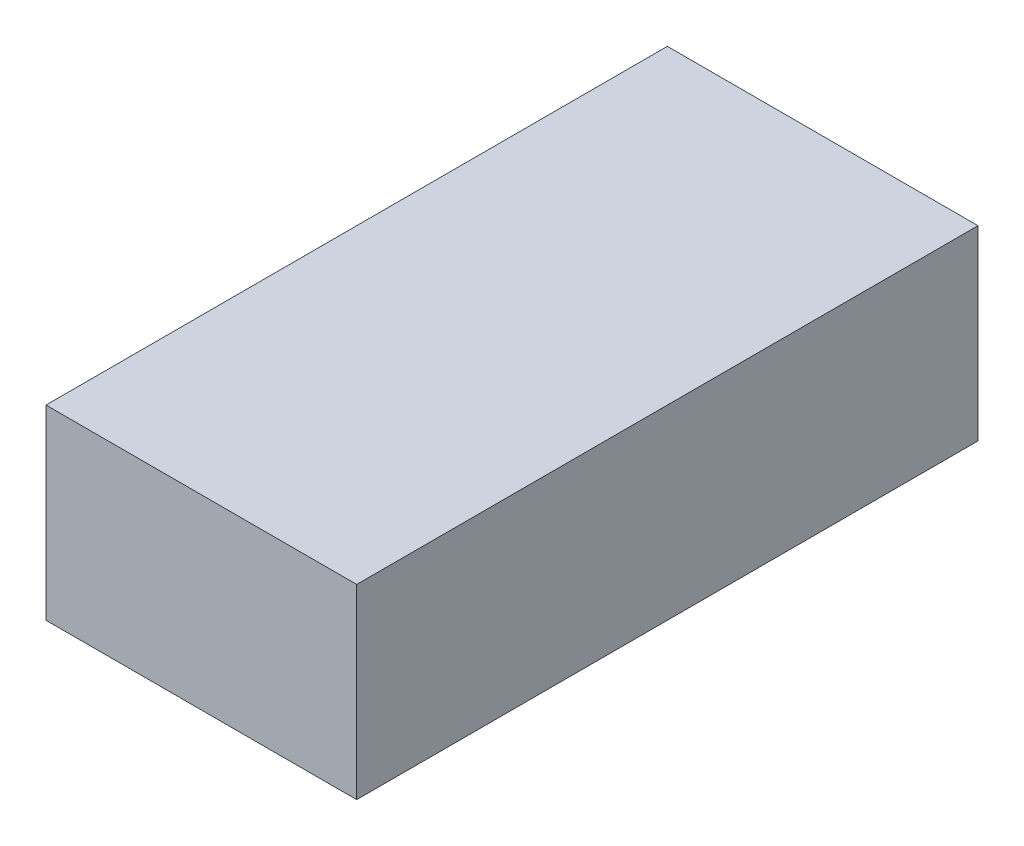
SolidWorks part; units mm, degrees
ref_plane "Front Plane" through (0, 0, 0) normal (0, 0, 1) x (1, 0, 0)
ref_plane "Top Plane" through (0, 0, 0) normal (0, 1, 0) x (1, 0, 0)
ref_plane "Right Plane" through (0, 0, 0) normal (1, 0, 0) x (0, 0, -1)
sketch "Sketch2" plane through (0, 0, 0) normal (1, 0, 0) x (0, 0, -1)
  line L3 (-262.7936, 0) -> (0, 0)
  line L4 (0, 0) -> (139.7, 0)
  line L6 (139.7, 0) -> (139.7, 81.9)
  line L7 (139.7, 81.9) -> (124.7, 81.9)
  line L8 (124.7, 81.9) -> (124.7, 20)
  line L9 (124.7, 20) -> (0, 20)
  line L10 (0, 20) -> (0, 133.7)
  line L11 (0, 133.7) -> (-115, 133.7)
  line L12 (-115, 133.7) -> (-171.1938, 94.3527)
  line L13 (-171.1938, 94.3527) -> (-262.7936, 81.4791)
  line L18 (-262.7936, 81.4791) -> (-262.7936, 31.4791)
  line L19 (-262.7936, 31.4791) -> (-262.7936, 0) construction
  arc A2 (-262.7936, 31.4791) -> (-262.7936, 0) centre (-255.1441, 15.7396) ccw
  dimension "D12" = 17.5
  dimension "D2" = 113.7
  dimension "D3" = 20
  dimension "D4" = 35
  dimension "D5" = 153
  dimension "D6" = 139.7
  dimension "D7" = 15
  dimension "D8" = 61.9
  dimension "D9" = 92.5
  dimension "D10" = 68.6
  dimension "D11" = 50
  dimension "D13" = 115
extrude "Boss-Extrude1" add sketch "Sketch2" along normal mid plane 138
sketch "Sketch4" plane through (0, 20, 0) normal (0, 1, 0) x (1, 0, 0)
  line L0 (69, 124.7) -> (-69, 124.7) construction
  line L1 (69, 0) -> (54, 0)
  line L2 (69, 0) -> (69, 124.7)
  line L3 (69, 124.7) -> (54, 124.7)
  line L4 (54, 0) -> (54, 124.7)
  dimension "D1" = 15
extrude "Boss-Extrude2" add sketch "Sketch4" along normal up to surface (61.9 mm away) up to face at (0, 81.9, -132.2)
mirror "Mirror1" about plane through (0, 0, 0) normal (1, 0, 0) of "Boss-Extrude2"
sketch "Sketch5" plane through (69, 0, 0) normal (1, 0, 0) x (0, 0, -1)
  line L0 (-262.7936, 0) -> (139.7, 0) construction
  line L1 (-224.9441, 0) -> (-160.3441, 0)
  line L2 (28.0559, 0) -> (92.6559, 0)
  arc A0 (-224.9441, 0) -> (-160.3441, 0) centre (-192.6441, 0) ccw
  arc A1 (28.0559, 0) -> (92.6559, 0) centre (60.3559, 0) ccw
  arc A2 (-262.7936, 31.4791) -> (-262.7936, 0) centre (-255.1441, 15.7396) ccw construction
  point P11 (-272.6441, 15.7396)
  dimension "D3" = 32.3
  dimension "D1" = 333
  dimension "D2" = 80
extrude "Boss-Extrude3" add sketch "Sketch5" against normal blind 20.4
mirror "Mirror2" about plane through (0, 0, 0) normal (1, 0, 0) of "Boss-Extrude3"
fillet "Fillet1" radius 10 5 edges at (0, 133.7, 0) (0, 133.7, 115) (0, 94.3527, 171.1938) (0, 81.4791, 262.7936) (0, 31.4791, 262.7936)
sketch "Sketch6" plane through (0, 0, 0) normal (1, 0, 0) x (0, 0, -1)
  line L1 (-2272.5135, -32.3) -> (7727.4865, -32.3)
  line L2 (-2272.5135, -32.3) -> (-2272.5135, 2967.7)
  line L3 (-2272.5135, 2967.7) -> (7727.4865, 2967.7)
  line L4 (7727.4865, -32.3) -> (7727.4865, 2967.7)
  arc A0 (-266.3756, 29.1598) -> (-262.7936, 0) centre (-255.1441, 15.7396) ccw construction
  arc A1 (-224.9441, 0) -> (-160.3441, 0) centre (-192.6441, 0) ccw construction
  point P7 (-272.5135, 13.6059)
  point P11 (-192.6441, -32.3)
  dimension "D1" = 3000
  dimension "D2" = 10000
  dimension "D3" = 2000
extrude "Boss-Extrude4" add sketch "Sketch6" along normal mid plane 5000 separate body
